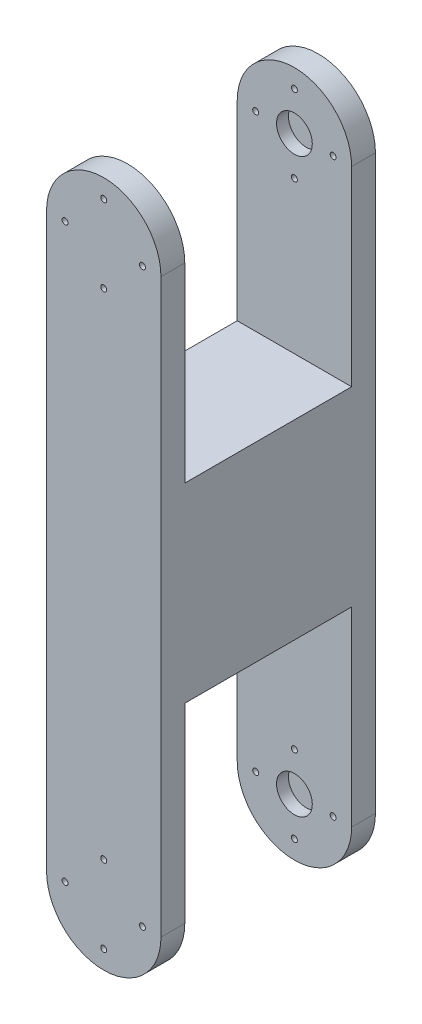
SolidWorks part; units mm, degrees
ref_plane "Front Plane" through (0, 0, 0) normal (0, 0, 1) x (1, 0, 0)
ref_plane "Top Plane" through (0, 0, 0) normal (0, 1, 0) x (1, 0, 0)
ref_plane "Right Plane" through (0, 0, 0) normal (1, 0, 0) x (0, 0, -1)
sketch "Sketch1" plane through (0, 0, 0) normal (0, 0, 1) x (1, 0, 0)
  line L0 (-15.24, 76.2) -> (-15.24, -76.2)
  line L1 (15.24, 76.2) -> (15.24, -76.2)
  line L2 (0, 91.44) -> (0, -91.44) construction
  arc A0 (-15.24, 76.2) -> (15.24, 76.2) centre (0, 76.2) cw
  arc A1 (-15.24, -76.2) -> (15.24, -76.2) centre (0, -76.2) ccw
  point P8 (0, 0)
  dimension "D1" = 30.48
  dimension "D2" = 152.4
extrude "Boss-Extrude1" add sketch "Sketch1" along normal blind 57.15
sketch "Sketch2" plane through (15.24, 0, 0) normal (1, 0, 0) x (0, 0, -1)
  line L0 (0, 91.44) -> (-57.15, 91.44) construction
  line L1 (-50.8, 91.44) -> (-6.35, 91.44)
  line L2 (-50.8, 91.44) -> (-50.8, 25.4)
  line L3 (-50.8, 25.4) -> (-6.35, 25.4)
  line L4 (-6.35, 91.44) -> (-6.35, 25.4)
  line L5 (-57.15, 91.44) -> (-50.8, 91.44) construction
  line L6 (-6.35, 91.44) -> (0, 91.44) construction
  dimension "D1" = 6.35
  dimension "D2" = 66.04
extrude "Cut-Extrude1" cut sketch "Sketch2" against normal blind 57.15
sketch "Sketch5" plane through (0, 0, 0) normal (0, 0, -1) x (-1, 0, 0)
  line L0 (-12.7, 76.2) -> (-15.24, 76.2) construction
  line L1 (-15.24, -76.2) -> (-15.24, 76.2) construction
  line L2 (0, 88.9) -> (0, 91.44) construction
  circle A0 centre (0, 76.2) radius 12.7
  arc A1 (15.24, 76.2) -> (-15.24, 76.2) centre (0, 76.2) ccw construction
  dimension "D1" = 25.4
sketch "Sketch6" plane through (0, 0, 6.35) normal (0, 0, 1) x (1, 0, 0)
  circle A0 centre (0, 76.2) radius 4.7625
  dimension "D1" = 9.525
extrude "Cut-Extrude3" cut sketch "Sketch6" against normal blind 3.175
ref_plane "Plane2" through (0, 0, 28.575) normal (0, 0, 1) x (1, 0, 0)
mirror "Mirror3" about plane through (0, 0, 28.575) normal (0, 0, 1) of "Cut-Extrude3"
sketch "Sketch7" plane through (0, 0, 0) normal (0, 0, -1) x (-1, 0, 0)
  circle A0 centre (0, 76.2) radius 10.3188
  circle A1 centre (0, 76.2) radius 12.7 construction
  dimension "D1" = 2.3812
sketch "Sketch8" plane through (0, 0, 0) normal (0, 0, -1) x (-1, 0, 0)
  circle A0 centre (0, 65.8812) radius 0.7937
  circle A1 centre (0, 76.2) radius 10.3188 construction
  circle A2 centre (-10.3188, 76.2) radius 0.7937
  circle A3 centre (0, 86.5187) radius 0.7937
  circle A4 centre (10.3188, 76.2) radius 0.7938
  point P13 (0, 76.2)
  dimension "D1" = 1.5875
  dimension "D2" = 4
extrude "Cut-Extrude4" cut sketch "Sketch8" against normal through all
mirror "Mirror7" about plane through (0, 0, 0) normal (0, 1, 0) of "Cut-Extrude4", "Cut-Extrude3", "Cut-Extrude1"
